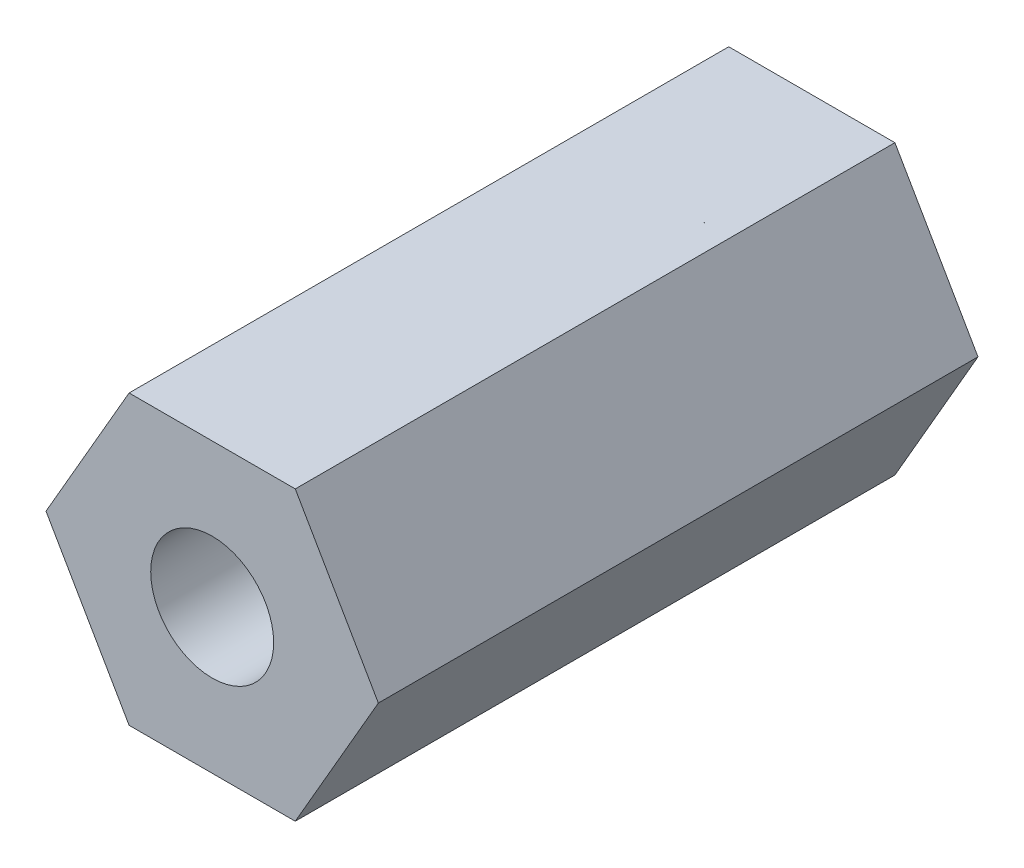
SolidWorks part; units mm, degrees
ref_plane "Front Plane" through (0, 0, 0) normal (0, 0, 1) x (1, 0, 0)
ref_plane "Top Plane" through (0, 0, 0) normal (0, 1, 0) x (1, 0, 0)
ref_plane "Right Plane" through (0, 0, 0) normal (1, 0, 0) x (0, 0, -1)
sketch "Sketch2" plane through (0, 0, 0) normal (0, 0, 1) x (1, 0, 0)
  line L0 (0, 0) -> (5.5426, 0) construction
  line L1 (5.5426, 0) -> (2.7713, 4.8)
  line L2 (2.7713, 4.8) -> (-2.7713, 4.8)
  line L3 (-2.7713, 4.8) -> (-5.5426, 0)
  line L4 (-5.5426, 0) -> (-2.7713, -4.8)
  line L5 (-2.7713, -4.8) -> (2.7713, -4.8)
  line L6 (2.7713, -4.8) -> (5.5426, 0)
  circle A0 centre (0, 0) radius 4.8 construction
  dimension "D1" = 9.6
extrude "Boss-Extrude1" add sketch "Sketch2" along normal blind 20
sketch "Sketch3" plane through (0, 0, 0) normal (0, 0, -1) x (-1, 0, 0)
  circle A0 centre (0, 0) radius 2.05
  dimension "D1" = 4.1
extrude "Cut-Extrude1" cut sketch "Sketch3" against normal up to surface (20 mm away) up to face at (0, 0, 20)
